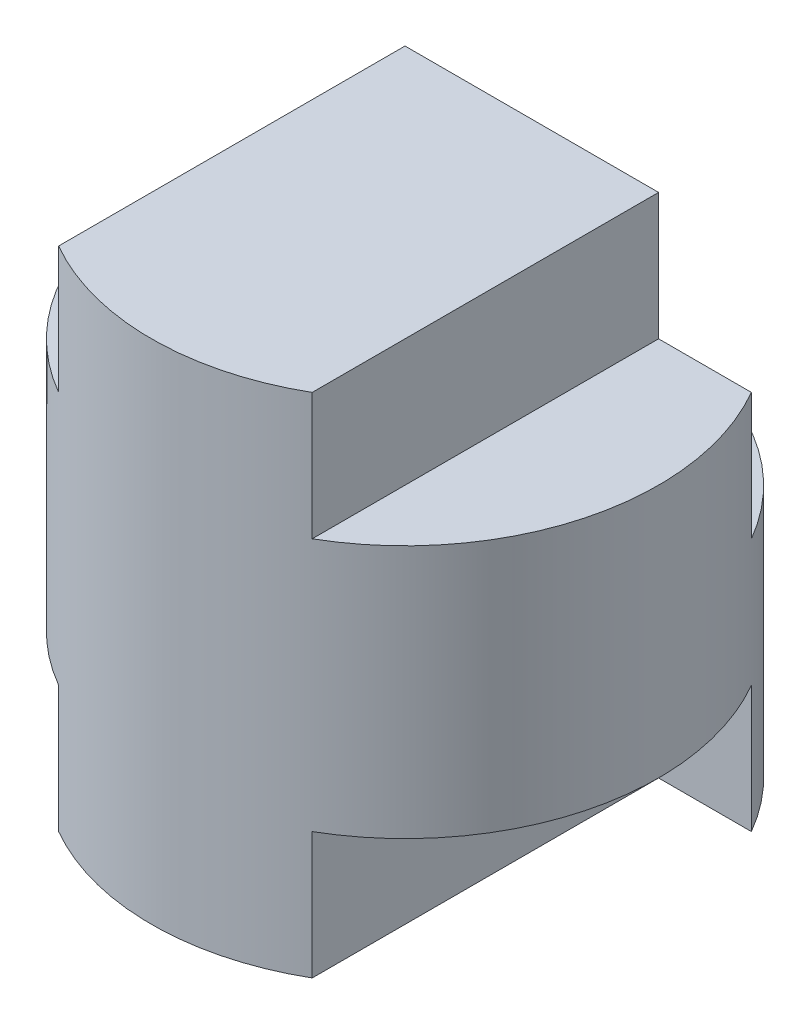
SolidWorks part; units mm, degrees
ref_plane "Front" through (0, 0, 0) normal (0, 0, 1) x (1, 0, 0)
ref_plane "Top" through (0, 0, 0) normal (0, 1, 0) x (1, 0, 0)
ref_plane "Right" through (0, 0, 0) normal (1, 0, 0) x (0, 0, -1)
sketch "Sketch1" plane through (0, 0, 0) normal (0, 1, 0) x (1, 0, 0)
  circle A0 centre (0, 0) radius 2
  dimension "D1" = 4
extrude "Boss-Extrude1" add sketch "Sketch1" along normal blind 4
sketch "Sketch2" plane through (0, 0, 0) normal (0, 0, 1) x (1, 0, 0)
  line L1 (-2, 4) -> (-1, 4)
  line L2 (-2, 4) -> (-2, 3)
  line L3 (-2, 3) -> (-1, 3)
  line L4 (-1, 4) -> (-1, 3)
  line L5 (2, 4) -> (1, 4)
  line L6 (2, 4) -> (2, 3)
  line L7 (2, 3) -> (1, 3)
  line L8 (1, 4) -> (1, 3)
  line L9 (2, 0) -> (1, 0)
  line L10 (2, 0) -> (2, 1)
  line L11 (2, 1) -> (1, 1)
  line L12 (1, 0) -> (1, 1)
  line L13 (-2, 0) -> (-1, 0)
  line L14 (-2, 0) -> (-2, 1)
  line L15 (-2, 1) -> (-1, 1)
  line L16 (-1, 0) -> (-1, 1)
  dimension "D1" = 1
  dimension "D2" = 1
  dimension "D3" = 1
  dimension "D4" = 1
  dimension "D5" = 1
  dimension "D6" = 1
  dimension "D7" = 1
  dimension "D8" = 1
extrude "Cut-Extrude1" cut sketch "Sketch2" against normal blind 1 and the other way blind 4 contours L13 L16 L15 L14 | L12 L9 L10 L11 | L5 L8 L7 L6 | L2 L1 L4 L3
sketch "Sketch3" plane through (0, 4, 0) normal (0, 1, 0) x (1, 0, 0)
  line L0 (-1.7321, 1) -> (1.7321, 1)
  arc A0 (-1.7321, 1) -> (1.7321, 1) centre (0, 0) cw
extrude "Cut-Extrude2" cut sketch "Sketch3" against normal blind 2
